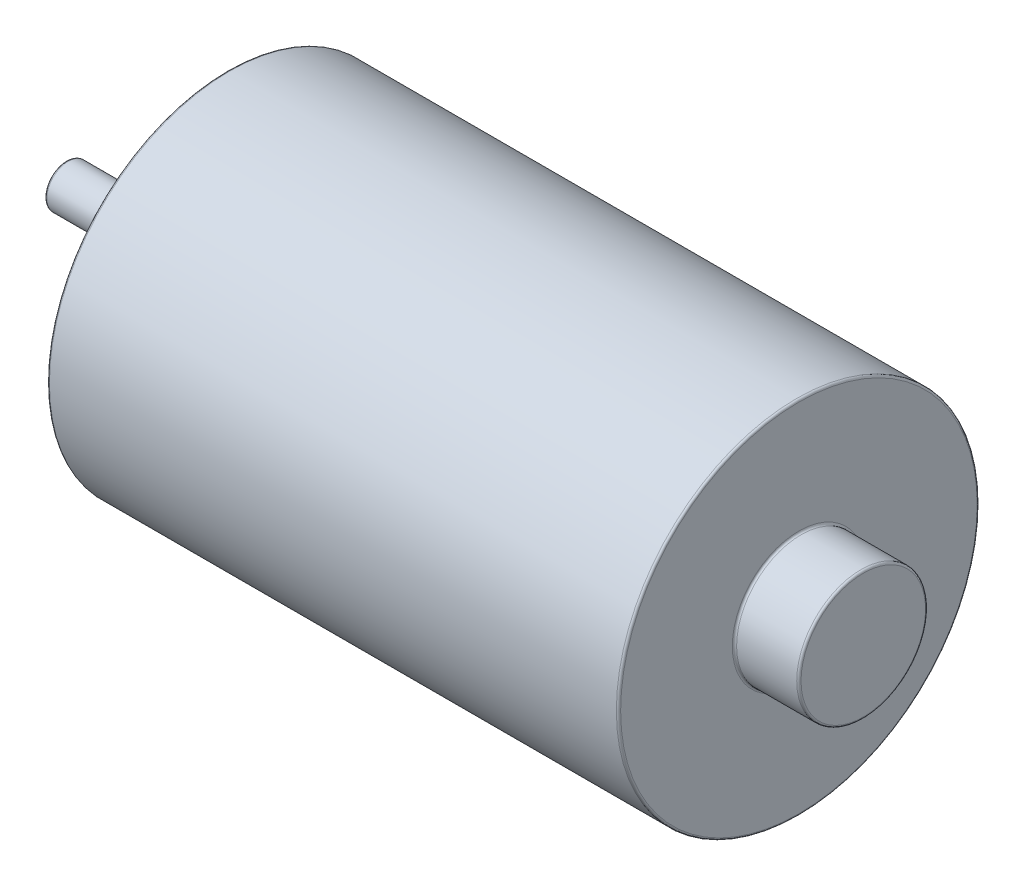
SolidWorks part; units mm, degrees
ref_plane "Front Plane" through (0, 0, 0) normal (0, 0, 1) x (1, 0, 0)
ref_plane "Top Plane" through (0, 0, 0) normal (0, 1, 0) x (1, 0, 0)
ref_plane "Right Plane" through (0, 0, 0) normal (1, 0, 0) x (0, 0, -1)
sketch "Sketch1" plane through (0, 0, 0) normal (0, 0, 1) x (1, 0, 0)
  line L0 (-47.8, 2.5) -> (-47.8, 0)
  line L1 (-33, 8.5) -> (-33, 2.5)
  line L2 (-29, 21) -> (-29, 8.5)
  line L3 (37.5, 21) -> (37.5, 7.5)
  line L4 (-47.8, 0) -> (45, 0) construction
  line L5 (37.5, 7.5) -> (45, 7.5)
  line L6 (-47.8, 2.5) -> (-33, 2.5)
  line L7 (-29, 21) -> (37.5, 21)
  line L8 (-33, 8.5) -> (-29, 8.5)
  line L9 (45, 7.5) -> (45, 0)
  line L10 (-47.8, 0) -> (45, 0)
  dimension "D1" = 66.5
  dimension "D2" = 7.5
  dimension "D3" = 4
  dimension "D4" = 74
  dimension "D5" = 78
  dimension "D6" = 14.8
revolve "Revolve1" add sketch "Sketch1" angle 360 about L4
fillet "Fillet1" radius 0.25 8 edges at (-33, 0, 2.5) (-47.8, 0, 2.5) (-33, 0, 8.5) (-29, 0, 8.5) (45, 0, 7.5) (37.5, 0, 7.5) (37.5, 0, 21) (-29, 0, 21)
sketch "Sketch4" plane through (-29, 0, 0) normal (-1, 0, 0) x (0, 0, 1)
  circle A0 centre (0, 14.5) radius 2
  circle A1 centre (0, -14.5) radius 2
extrude "Cut-Extrude2" cut sketch "Sketch4" against normal blind 10
